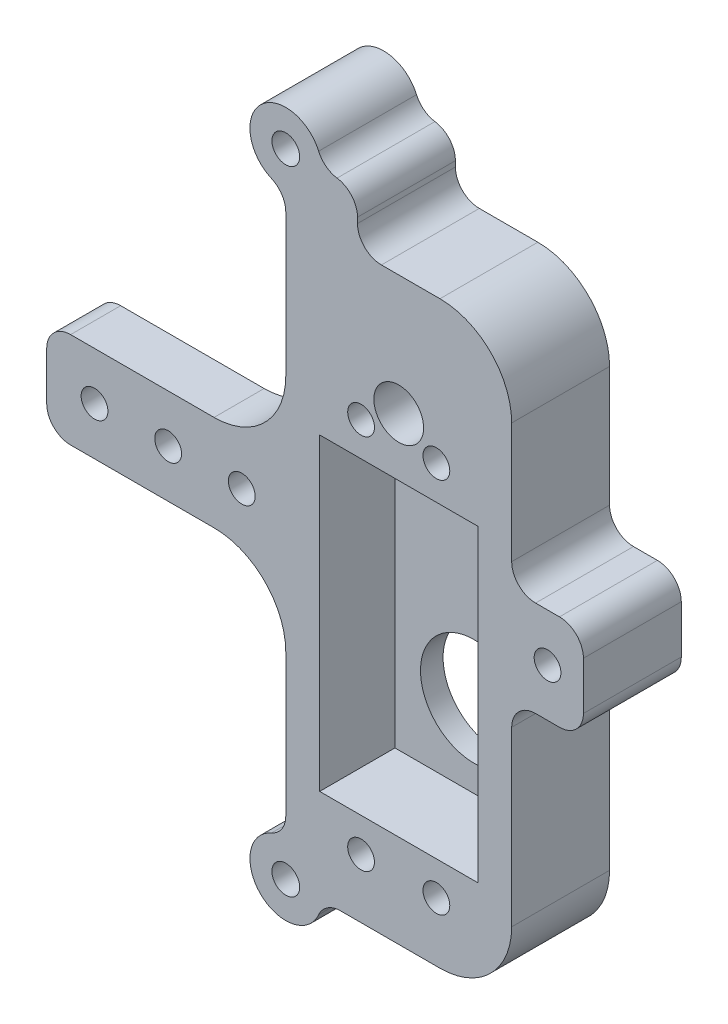
SolidWorks part; units mm, degrees
ref_plane "Front" through (0, 0, 0) normal (0, 0, 1) x (1, 0, 0)
ref_plane "Top" through (0, 0, 0) normal (0, 1, 0) x (1, 0, 0)
ref_plane "Right" through (0, 0, 0) normal (1, 0, 0) x (0, 0, -1)
sketch "Sketch1" plane through (0, 0, 0) normal (0, 0, 1) x (1, 0, 0)
  line L1 (0, 0) -> (31.75, 0)
  line L2 (0, 0) -> (0, 12.7)
  line L3 (0, 12.7) -> (31.75, 12.7)
  line L4 (31.75, 0) -> (31.75, 12.7)
  line L5 (31.75, 41.35) -> (61.75, 41.35)
  line L6 (31.75, 41.35) -> (31.75, -28.65)
  line L7 (31.75, -28.65) -> (61.75, -28.65)
  line L8 (61.75, 41.35) -> (61.75, -28.65)
  line L9 (31.75, -28.65) -> (61.75, -28.65)
  line L10 (31.75, -28.65) -> (31.75, -35.65)
  line L11 (31.75, -35.65) -> (61.75, -35.65)
  line L12 (61.75, -28.65) -> (61.75, -35.65)
  line L13 (61.75, 0) -> (71.275, 0)
  line L14 (61.75, 0) -> (61.75, 12.7)
  line L15 (61.75, 12.7) -> (71.275, 12.7)
  line L16 (71.275, 0) -> (71.275, 12.7)
  point P9 (31.75, 6.35)
  point P10 (31.75, 6.35)
  point P18 (71.275, 6.35)
  point P19 (61.75, 6.35)
  dimension "D1" = 31.75
  dimension "D2" = 12.7
  dimension "D3" = 70
  dimension "D4" = 30
  dimension "D5" = 7
  dimension "D6" = 9.525
extrude "Boss-Extrude1" add sketch "Sketch1" along normal blind 13 contours L8 L5 L6 L4 L7 | L1 L4 L3 L2 | L10 L9 L12 L11
sketch "Sketch4" plane through (0, 0, 13) normal (0, 0, 1) x (1, 0, 0)
  line L0 (61.75, 41.35) -> (61.75, -35.65) construction
  line L1 (31.75, 41.35) -> (61.75, 41.35) construction
  line L2 (31.75, -35.65) -> (61.75, -35.65) construction
  circle A0 centre (41.75, 22.2) radius 1.778
  circle A1 centre (51.75, 22.2) radius 1.778
  circle A2 centre (41.75, -27.8) radius 1.778
  circle A3 centre (51.75, -27.8) radius 1.778
  point P10 (61.75, 2.85)
  point P13 (46.75, -35.65)
  point P16 (46.75, 41.35)
  dimension "D1" = 10
  dimension "D4" = 30.65
  dimension "D5" = 3.556
  dimension "D6" = 5
  dimension "D7" = 5
  dimension "D2" = 10
  dimension "D3" = 50
extrude "Cut-Extrude3" cut sketch "Sketch4" against normal through all
sketch "Sketch5" plane through (0, 0, 13) normal (0, 0, 1) x (1, 0, 0)
  line L0 (61.75, 41.35) -> (61.75, -35.65) construction
  line L1 (36.25, 17.7) -> (57.25, 17.7)
  line L2 (36.25, 17.7) -> (36.25, -23.3)
  line L3 (36.25, -23.3) -> (57.25, -23.3)
  line L4 (57.25, 17.7) -> (57.25, -23.3)
  line L6 (31.75, 41.35) -> (61.75, 41.35) construction
  point P7 (61.75, 2.85)
  point P8 (46.75, -23.3)
  point P13 (46.75, 41.35)
  dimension "D1" = 21
  dimension "D2" = 41
  dimension "D3" = 26.15
extrude "Cut-Extrude4" cut sketch "Sketch5" against normal blind 10
sketch "Sketch6" plane through (0, 0, 3) normal (0, 0, 1) x (1, 0, 0)
  line L0 (36.25, -23.3) -> (57.25, -23.3) construction
  circle A0 centre (46.75, -12.7) radius 7.112
  circle A1 centre (51.75, -27.8) radius 1.778 construction
  point P7 (46.75, -23.3)
  dimension "D1" = 14.224
  dimension "D2" = 15.1
extrude "Cut-Extrude5" cut sketch "Sketch6" against normal through all
sketch "Sketch7" plane through (0, 0, 0) normal (0, 0, -1) x (-1, 0, 0)
  line L1 (0, 0) -> (-31.75, 0)
  line L2 (0, 0) -> (0, 12.7)
  line L3 (0, 12.7) -> (-31.75, 12.7)
  line L4 (-31.75, 0) -> (-31.75, 12.7)
extrude "Cut-Extrude6" cut sketch "Sketch7" against normal blind 6.35
sketch "Sketch8" plane through (0, 0, 6.35) normal (0, 0, -1) x (-1, 0, 0)
  line L0 (0, 0) -> (0, 12.7) construction
  circle A0 centre (-6.35, 6.35) radius 1.778
  circle A1 centre (-25.908, 6.35) radius 1.778
  circle A2 centre (-16.129, 6.35) radius 1.778
  point P6 (0, 6.35)
  dimension "D1" = 19.558
  dimension "D3" = 3.556
  dimension "D4" = 3.556
  dimension "D5" = 3.556
  dimension "D2" = 6.35
  dimension "D6" = 9.779
extrude "Cut-Extrude7" cut sketch "Sketch8" against normal through all
sketch "Sketch10" plane through (0, 0, 0) normal (0, 0, -1) x (-1, 0, 0)
  line L0 (-31.75, 41.35) -> (-61.75, 41.35) construction
  line L1 (0, 0) -> (0, 12.7) construction
  circle A0 centre (-46.75, 25.4) radius 1.905
  point P6 (-46.75, 41.35)
  point P7 (0, 6.35)
  dimension "D1" = 3.81
  dimension "D2" = 19.05
extrude "Cut-Extrude8" cut sketch "Sketch10" against normal through all
sketch "Sketch11" plane through (0, 0, 13) normal (0, 0, 1) x (1, 0, 0)
  circle A0 centre (46.75, 25.4) radius 3.302
  dimension "D1" = 6.604
extrude "Cut-Extrude9" cut sketch "Sketch11" against normal blind 9.525
sketch "Sketch13" plane through (0, 0, 13) normal (0, 0, 1) x (1, 0, 0)
  line L0 (61.75, 41.35) -> (61.75, -35.65) construction
  line L1 (61.75, 0) -> (71.275, 0)
  line L2 (61.75, 0) -> (61.75, 12.7)
  line L3 (61.75, 12.7) -> (71.275, 12.7)
  line L4 (71.275, 0) -> (71.275, 12.7)
  line L5 (0, 12.7) -> (31.75, 12.7) construction
  circle A0 centre (66.5125, 6.35) radius 1.778
  dimension "D3" = 3.556
  dimension "D1" = 12.7
  dimension "D2" = 9.525
  dimension "D4" = 4.7625
  dimension "D5" = 6.35
extrude "Boss-Extrude2" add sketch "Sketch13" against normal up to surface (13 mm away) up to face at (44.845, 25.4, 0)
sketch "Sketch15" plane through (0, 0, 0) normal (0, 0, -1) x (-1, 0, 0)
  circle A0 centre (-46.75, 25.4) radius 21.209
  circle A1 centre (-46.75, -12.7) radius 21.209
  dimension "D1" = 42.418
  dimension "D2" = 42.418
sketch "Sketch17" plane through (0, 0, 13) normal (0, 0, 1) x (1, 0, 0)
  line L1 (31.75, 41.35) -> (41.275, 41.35)
  line L2 (31.75, 41.35) -> (31.75, 48.3592)
  line L3 (31.75, 48.3592) -> (41.275, 48.3592)
  line L4 (41.275, 41.35) -> (41.275, 48.3592)
  circle A0 centre (31.75, 48.3592) radius 4.7625
  circle A1 centre (31.75, -35.65) radius 4.7625
  line M16 (61.75, 41.35) -> (31.75, 41.35)
  line M21 (31.75, 0) -> (31.75, -35.65)
  line M22 (31.75, -35.65) -> (61.75, -35.65)
  dimension "D3" = 9.525
  dimension "D4" = 9.525
  dimension "D1" = 7.0092
  dimension "D2" = 9.525
extrude "Boss-Extrude3" add sketch "Sketch17" against normal up to surface (13 mm away) contours L3 A0 L2 | A0 L2 L4 L3 M16 | A1 M21 M22
sketch "Sketch18" plane through (0, 0, 13) normal (0, 0, 1) x (1, 0, 0)
  circle A0 centre (31.75, -35.65) radius 1.8415
  circle A1 centre (31.75, 48.3592) radius 1.8415
  dimension "D1" = 3.683
  dimension "D2" = 3.683
extrude "Cut-Extrude10" cut sketch "Sketch18" against normal through all
fillet "Fillet1" radius 9.525 4 edges at (31.75, 0, 9.675) (31.75, 12.7, 9.675) (61.75, 41.35, 6.5) (61.75, -35.65, 6.5)
fillet "Fillet2" radius 3.175 9 edges at (71.275, 0, 6.5) (71.275, 12.7, 6.5) (61.75, 12.7, 6.5) (61.75, 0, 6.5) (31.75, -30.8875, 6.5) (36.5125, -35.65, 6.5) (31.75, 43.5967, 6.5) (41.275, 41.35, 6.5) (36.5125, 48.3592, 6.5)
fillet "Fillet3" radius 3.175 3 edges at (41.275, 48.3592, 6.5) (0, 12.7, 9.675) (0, 0, 9.675)
